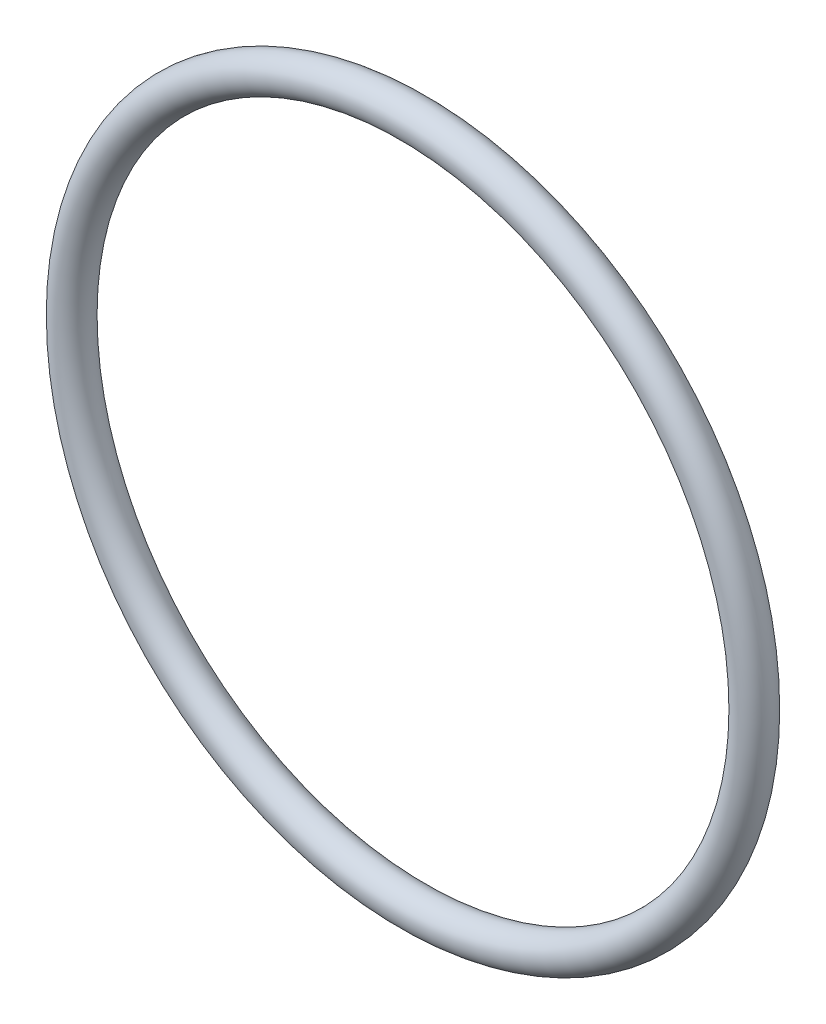
SolidWorks part; units mm, degrees
material "Caoutchouc silicone"
ref_plane "Plan de face" through (0, 0, 0) normal (0, 0, 1) x (1, 0, 0)
ref_plane "Plan de dessus" through (0, 0, 0) normal (0, 1, 0) x (1, 0, 0)
ref_plane "Plan de droite" through (0, 0, 0) normal (1, 0, 0) x (0, 0, -1)
sketch "Esquisse1" plane through (0, 0, 0) normal (1, 0, 0) x (0, 0, -1)
  line L0 (0, 13.5) -> (0, 0) construction
  line L1 (0, 0) -> (5.5178, 0) construction
  circle A0 centre (0, 14.25) radius 0.75
  dimension "D2" = 1.5
  dimension "D1" = 13.5
revolve "Révolution1" add sketch "Esquisse1" angle 360 about L1
